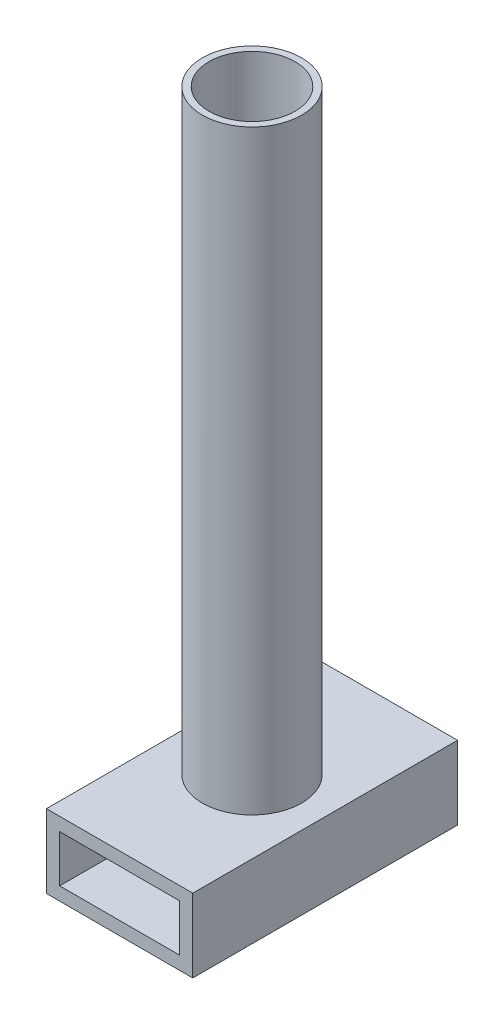
SolidWorks part; units mm, degrees
ref_plane "Front Plane" through (0, 0, 0) normal (0, 0, 1) x (1, 0, 0)
ref_plane "Top Plane" through (0, 0, 0) normal (0, 1, 0) x (1, 0, 0)
ref_plane "Right Plane" through (0, 0, 0) normal (1, 0, 0) x (0, 0, -1)
sketch "Sketch1" plane through (0, 0, 0) normal (0, 0, 1) x (1, 0, 0)
  line L0 (-11.05, 5.55) -> (11.05, 5.55)
  line L1 (-9.05, -3.55) -> (9.05, -3.55)
  line L2 (-9.05, -3.55) -> (-9.05, 3.55)
  line L3 (-9.05, 3.55) -> (9.05, 3.55)
  line L4 (9.05, -3.55) -> (9.05, 3.55)
  line L7 (11.05, -5.55) -> (11.05, 5.55)
  line L8 (-11.05, -5.55) -> (11.05, -5.55)
  line L9 (-11.05, -5.55) -> (-11.05, 5.55)
  point P0 (0, 0)
  dimension "D1" = 18.1
  dimension "D2" = 7.1
  dimension "D3" = 2
extrude "Boss-Extrude1" add sketch "Sketch1" along normal blind 40
sketch "Sketch2" plane through (0, -5.55, 0) normal (0, -1, 0) x (1, 0, 0)
  circle A0 centre (0, 20) radius 1.5
  point P4 (0, 20)
  dimension "D1" = 3
extrude "Cut-Extrude1" cut sketch "Sketch2" against normal blind 33
sketch "Sketch3" plane through (0, 5.55, 0) normal (0, 1, 0) x (1, 0, 0)
  line L0 (11.05, 0) -> (-11.05, 0) construction
  line L1 (-11.05, -40) -> (-11.05, 0) construction
  circle A0 centre (0, -20) radius 7.5
  circle A1 centre (0, -20) radius 6.5
  point P0 (0, -20)
  dimension "D3" = 15
  dimension "D1" = 20
  dimension "D2" = 11.05
  dimension "D4" = 1
extrude "Boss-Extrude3" add sketch "Sketch3" along normal blind 90
